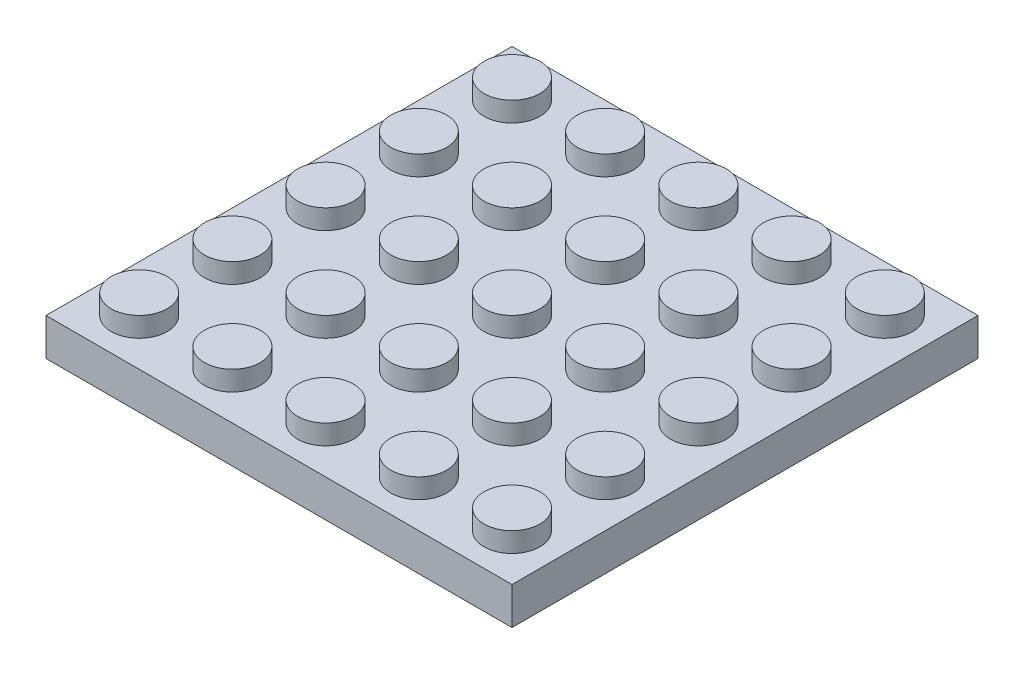
SolidWorks part; units mm, degrees
ref_plane "前基準面" through (0, 0, 0) normal (0, 0, 1) x (1, 0, 0)
ref_plane "上基準面" through (0, 0, 0) normal (0, 1, 0) x (1, 0, 0)
ref_plane "右基準面" through (0, 0, 0) normal (1, 0, 0) x (0, 0, -1)
sketch "草圖1" plane through (0, 0, 0) normal (0, 1, 0) x (1, 0, 0)
  line L1 (-4, -4) -> (4, -4)
  line L2 (-4, -4) -> (-4, 4)
  line L3 (-4, 4) -> (4, 4)
  line L4 (4, -4) -> (4, 4)
  line L5 (-4, -4) -> (4, 4) construction
  line L6 (-4, 4) -> (4, -4) construction
  point P0 (0, 0)
  dimension "width" = 8
  dimension "length" = 8
extrude "height" add sketch "草圖1" along normal blind 3.2
sketch "草圖2" plane through (0, 3.2, 0) normal (0, 1, 0) x (1, 0, 0)
  circle A0 centre (0, 0) radius 2.4
  dimension "D1" = 4.8
extrude "填料-伸長2" add sketch "草圖2" along normal blind 1.7
pattern_linear "直線複製排列1" count 5 spacing 8 along (1, 0, 0) count 5 spacing 8 along (0, 0, 1) of "height", "填料-伸長2"
shell "薄殼1" thickness 1.6
sketch "草圖3" plane through (0, 1.6, 0) normal (0, -1, 0) x (1, 0, 0)
  line L1 (0, 0) -> (8, 0) construction
  line L2 (0, 0) -> (0, 8) construction
  line L3 (0, 8) -> (8, 8) construction
  line L4 (8, 0) -> (8, 8) construction
  line L5 (0, 0) -> (8, 8) construction
  line L6 (0, 8) -> (8, 0) construction
  circle A0 centre (4, 4) radius 2.4
  circle A1 centre (4, 4) radius 3.255
  point P0 (4, 4)
  dimension "D1" = 4.8
  dimension "D2" = 6.51
extrude "填料-伸長3" add sketch "草圖3" along normal up to surface (1.6 mm away) up to face at (16, 0, 16)
pattern_linear "直線複製排列2" count 4 spacing 8 along (0, 0, 1) count 4 spacing 8 along (1, 0, 0) of "填料-伸長3"
